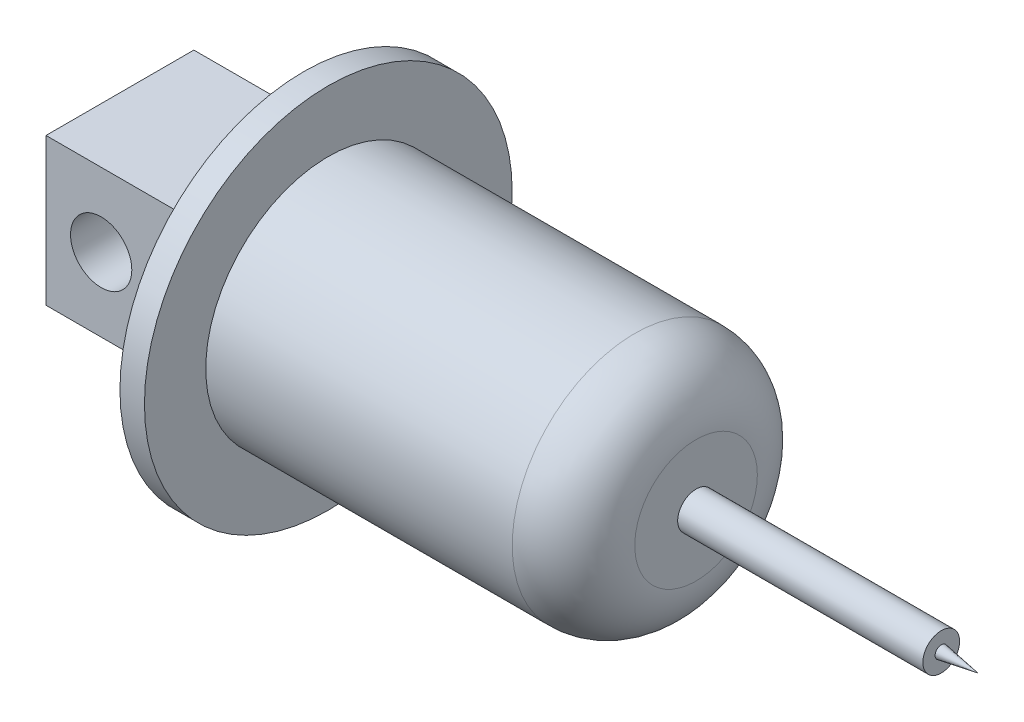
SolidWorks part; units mm, degrees
ref_plane "Front Plane" through (0, 0, 0) normal (0, 0, 1) x (1, 0, 0)
ref_plane "Top Plane" through (0, 0, 0) normal (0, 1, 0) x (1, 0, 0)
ref_plane "Right Plane" through (0, 0, 0) normal (1, 0, 0) x (0, 0, -1)
sketch "Sketch1" plane through (0, 0, 0) normal (0, 0, 1) x (1, 0, 0)
  circle A0 centre (0, 0) radius 10
  dimension "D1" = 20
extrude "Boss-Extrude1" add sketch "Sketch1" along normal blind 30
sketch "Sketch4" plane through (0, 0, 0) normal (0, 0, -1) x (-1, 0, 0)
  circle A0 centre (0, 0) radius 15
  dimension "D1" = 30
extrude "Boss-Extrude2" add sketch "Sketch4" along normal blind 2
fillet "Fillet1" radius 5 1 edges at (10, 0, 30)
sketch "Sketch6" plane through (0, 0, 30) normal (0, 0, 1) x (1, 0, 0)
  circle A0 centre (0, 0) radius 1.5
  dimension "D1" = 3
extrude "Boss-Extrude3" add sketch "Sketch6" along normal blind 20
sketch "Sketch7" plane through (0, 0, -2) normal (0, 0, -1) x (-1, 0, 0)
  line L1 (6.0313, -6) -> (-6.0313, -6)
  line L2 (6.0313, -6) -> (6.0313, 6)
  line L3 (6.0313, 6) -> (-6.0313, 6)
  line L4 (-6.0313, -6) -> (-6.0313, 6)
  line L5 (6.0313, -6) -> (-6.0313, 6) construction
  line L6 (6.0313, 6) -> (-6.0313, -6) construction
  point P0 (0, 0)
  dimension "D1" = 12
extrude "Boss-Extrude4" add sketch "Sketch7" along normal blind 15
sketch "Sketch8" plane through (-6.0313, 0, 0) normal (-1, 0, 0) x (0, 0, 1)
  line L0 (-17, -6) -> (-17, 6) construction
  circle A0 centre (-12.5, 0) radius 2.5
  dimension "D1" = 5
  dimension "D2" = 4.5
extrude "Cut-Extrude2" cut sketch "Sketch8" against normal through all
sketch "Sketch9" plane through (-6.0313, 0, 0) normal (-1, 0, 0) x (0, 0, 1)
  point P0 (-12.5, 0)
  point P1 (-7.4787, 8.3262)
sketch "Sketch10" plane through (0, 0, 0) normal (1, 0, 0) x (0, 0, -1)
  point P0 (12.5, 0)
ref_plane "Plane2" through (0, 0, 50) normal (0, 0, -1) x (-1, 0, 0)
sketch "Sketch11" plane through (0, 0, 50) normal (0, 0, -1) x (-1, 0, 0)
  point P0 (0, 0)
sketch "Sketch12" plane through (0, 0, 50) normal (0, 0, 1) x (1, 0, 0)
  circle A0 centre (0, 0) radius 0.65
  dimension "D1" = 1.3
sketch "Sketch15" plane through (0, 0, 0) normal (0, 1, 0) x (1, 0, 0)
  line L0 (0, -50) -> (0, -56.1541) construction
  line L1 (-0.65, -50) -> (0.65, -50) construction
  line L2 (0.5, -50) -> (0, -53)
  line L3 (-1.5, -50) -> (1.5, -50) construction
  line L4 (0, -53) -> (0, -50)
  line L5 (0, -50) -> (0.5, -50)
  dimension "D1" = 3
  dimension "D2" = 0.5
revolve "Revolve2" add sketch "Sketch15" angle 360 about L0
sketch "Sketch18" plane through (0, 0, 50) normal (0, 0, 1) x (1, 0, 0)
  point P0 (0, 0)
move or copy body "Body-Move/Copy3" bodies to move or copy 117 copy no translate (0, 0, -50)
move or copy body "Body-Move/Copy5" bodies to move or copy 120 copy no rotation origin (0, 0, 0) rotation axis (0, 1, 0) rotation angle 90
